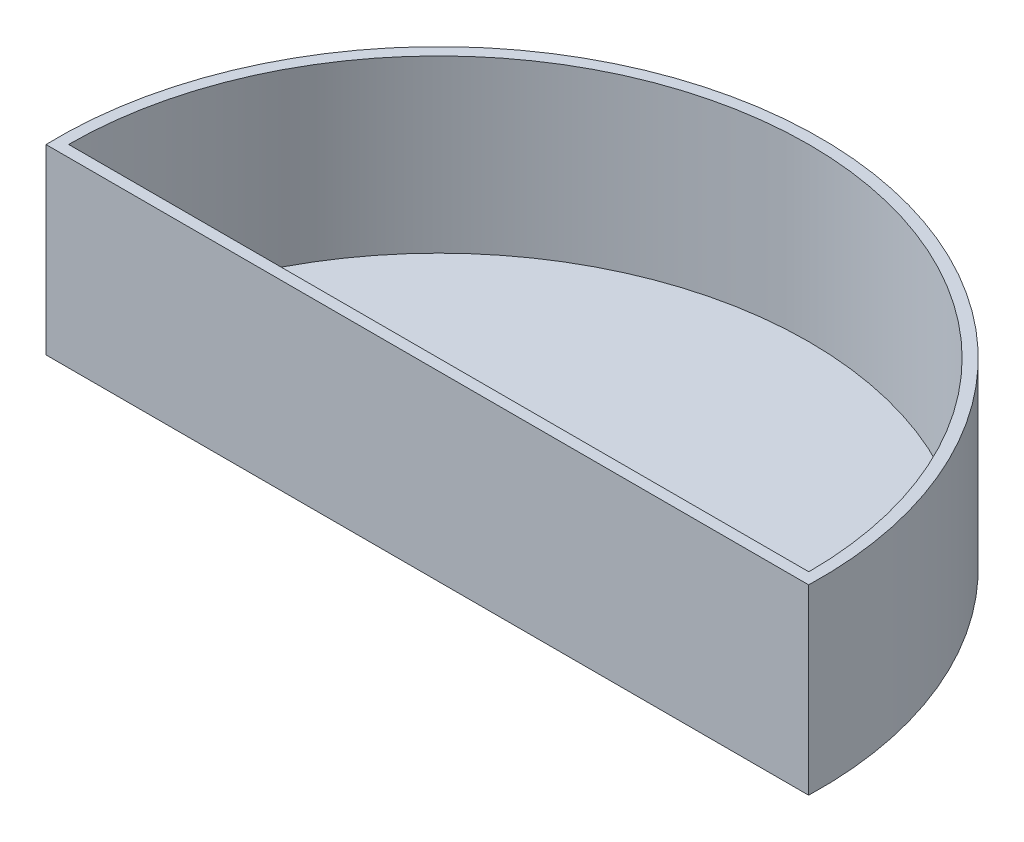
SolidWorks part; units mm, degrees
ref_plane "Front Plane" through (0, 0, 0) normal (0, 0, 1) x (1, 0, 0)
ref_plane "Top Plane" through (0, 0, 0) normal (0, 1, 0) x (1, 0, 0)
ref_plane "Right Plane" through (0, 0, 0) normal (1, 0, 0) x (0, 0, -1)
sketch "Sketch1" plane through (0, 0, 0) normal (0, 1, 0) x (1, 0, 0)
  line L0 (-13, 0) -> (-9, 0)
  line L1 (9, 0) -> (13, 0)
  circle A0 centre (0, 0) radius 12.43 construction
  circle A1 centre (0, 0) radius 9.43 construction
  circle A2 centre (0, 0) radius 13 construction
  circle A3 centre (0, 0) radius 9 construction
  arc A4 (9, 0) -> (-9, 0) centre (0, 0) ccw
  arc A5 (13, 0) -> (-13, 0) centre (0, 0) ccw
  dimension "D1" = 18.86
  dimension "D2" = 24.86
  dimension "D3" = 26
  dimension "D4" = 18
sketch "Sketch2" plane through (0, 0, 0) normal (0, 1, 0) x (1, 0, 0)
  line L0 (-13, 0) -> (13, 0)
  arc A0 (13, 0) -> (-13, 0) centre (0, 0) ccw construction
  arc A1 (13, 0) -> (-13, 0) centre (0, 0) ccw
sketch "Sketch3" plane through (0, 0, 0) normal (0, 1, 0) x (1, 0, 0)
  line L1 (-13, 0) -> (13, 0) construction
  line L2 (-13.394, -0.4) -> (13.394, -0.4)
  line L3 (-13.394, -0.4) -> (13.394, -0.4)
  line L4 (-13, 0) -> (13, 0)
  arc A2 (13, 0) -> (-13, 0) centre (0, 0) ccw construction
  arc A3 (13.394, -0.4) -> (-13.394, -0.4) centre (0, 0) ccw
  arc A4 (13.394, -0.4) -> (-13.394, -0.4) centre (0, 0) ccw
  arc A5 (13, 0) -> (-13, 0) centre (0, 0) ccw
  dimension "D1" = 0.4
extrude "Boss-Extrude2" add sketch "Sketch3" along normal blind 6
sketch "Sketch4" plane through (0, 0, 0) normal (0, -1, 0) x (1, 0, 0)
  line L0 (-13.394, 0.4) -> (13.394, 0.4) construction
  line L1 (-13.394, 0.4) -> (13.394, 0.4)
  arc A0 (-13.394, 0.4) -> (13.394, 0.4) centre (0, 0) ccw construction
  arc A1 (-13.394, 0.4) -> (13.394, 0.4) centre (0, 0) ccw
extrude "Boss-Extrude3" add sketch "Sketch4" along normal blind 0.4
